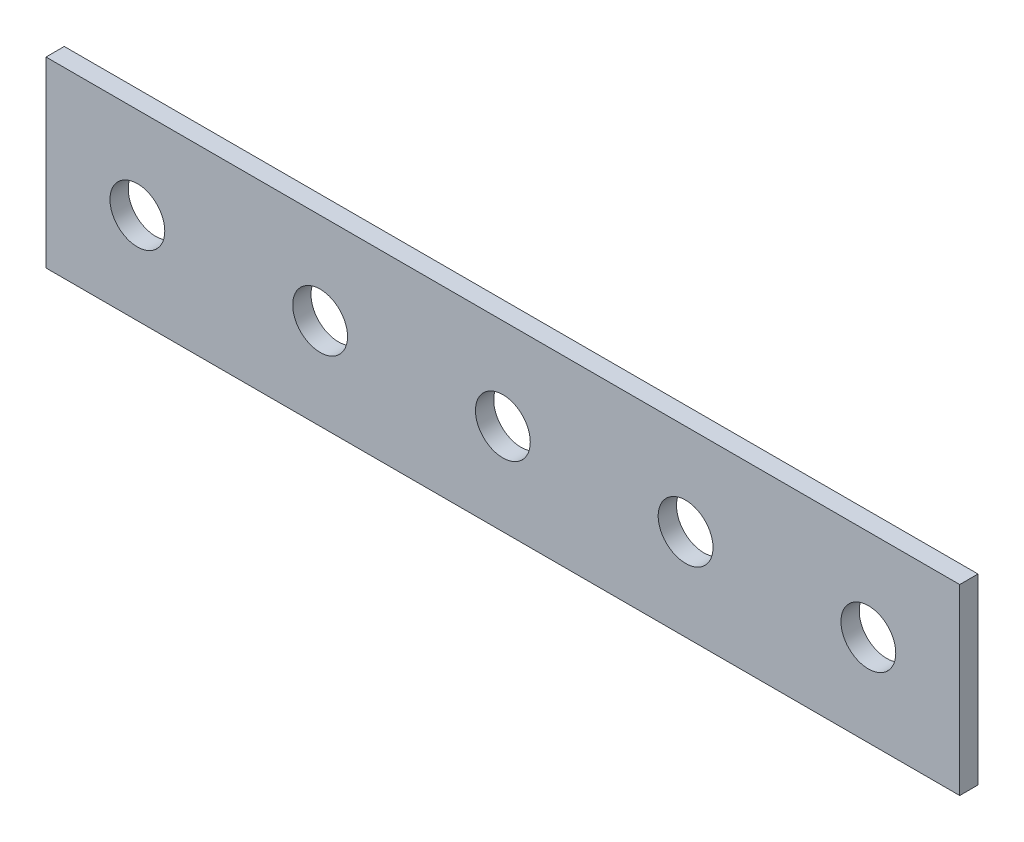
SolidWorks part; units mm, degrees
ref_plane "Front Plane" through (0, 0, 0) normal (0, 0, 1) x (1, 0, 0)
ref_plane "Top Plane" through (0, 0, 0) normal (0, 1, 0) x (1, 0, 0)
ref_plane "Right Plane" through (0, 0, 0) normal (1, 0, 0) x (0, 0, -1)
sketch "Esquisse1" plane through (0, 0, 0) normal (0, 0, 1) x (1, 0, 0)
  line L1 (0, 0) -> (50, 0)
  line L2 (0, 0) -> (0, 10)
  line L3 (0, 10) -> (50, 10)
  line L4 (50, 0) -> (50, 10)
  dimension "D1" = 10
  dimension "D2" = 50
extrude "Main" add sketch "Esquisse1" along normal blind 1
sketch "Esquisse2" plane through (0, 0, 1) normal (0, 0, 1) x (1, 0, 0)
  line L0 (50, 10) -> (0, 10) construction
  line L1 (50, 0) -> (50, 10) construction
  circle A0 centre (25, 5) radius 1.5
  point P5 (25, 10)
  point P10 (50, 5)
  dimension "D1" = 3
extrude "Hole" cut sketch "Esquisse2" against normal through all
pattern_linear "RepeatHoleRight" count 3 spacing 10 along (1, 0, 0) of "Hole"
pattern_linear "RepeatHoleLeft" count 3 spacing 10 along (-1, 0, 0) of "Hole"
